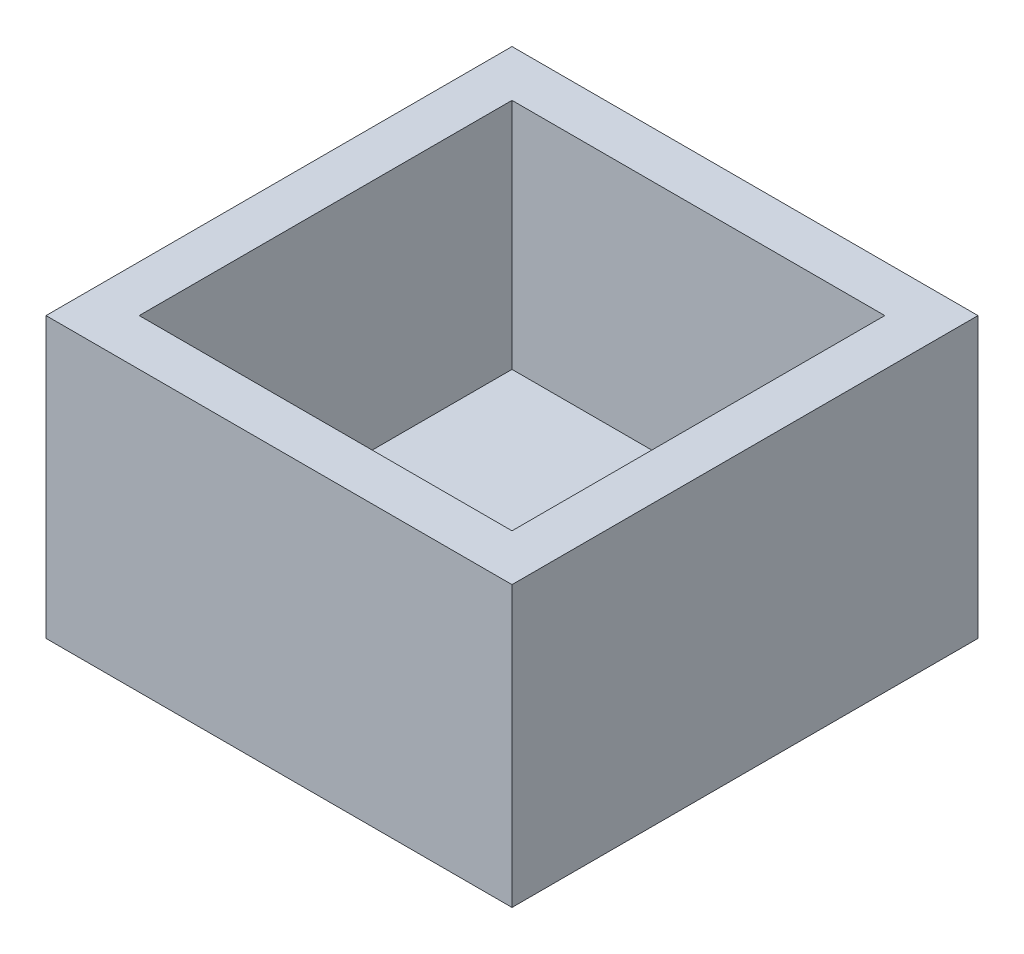
SolidWorks part; units mm, degrees
ref_plane "Front Plane" through (0, 0, 0) normal (0, 0, 1) x (1, 0, 0)
ref_plane "Top Plane" through (0, 0, 0) normal (0, 1, 0) x (1, 0, 0)
ref_plane "Right Plane" through (0, 0, 0) normal (1, 0, 0) x (0, 0, -1)
sketch "Sketch1" plane through (0, 0, 0) normal (0, 1, 0) x (1, 0, 0)
  line L1 (0, 0) -> (10, 0)
  line L2 (0, 0) -> (0, -10)
  line L3 (0, -10) -> (10, -10)
  line L4 (10, 0) -> (10, -10)
  dimension "D1" = 10
  dimension "D2" = 10
extrude "Boss-Extrude1" add sketch "Sketch1" along normal blind 1
sketch "Sketch2" plane through (0, 1, 0) normal (0, 1, 0) x (1, 0, 0)
  line L0 (10, 0) -> (0, 0) construction
  line L1 (0, 0) -> (10, 0)
  line L2 (0, 0) -> (0, -10)
  line L3 (0, -10) -> (10, -10)
  line L4 (10, 0) -> (10, -10)
  line L5 (1, -1) -> (9, -1)
  line L6 (1, -1) -> (1, -9)
  line L7 (1, -9) -> (9, -9)
  line L8 (9, -1) -> (9, -9)
  dimension "D1" = 1
  dimension "D2" = 1
  dimension "D3" = 8
  dimension "D4" = 8
extrude "Boss-Extrude2" add sketch "Sketch2" along normal blind 5
